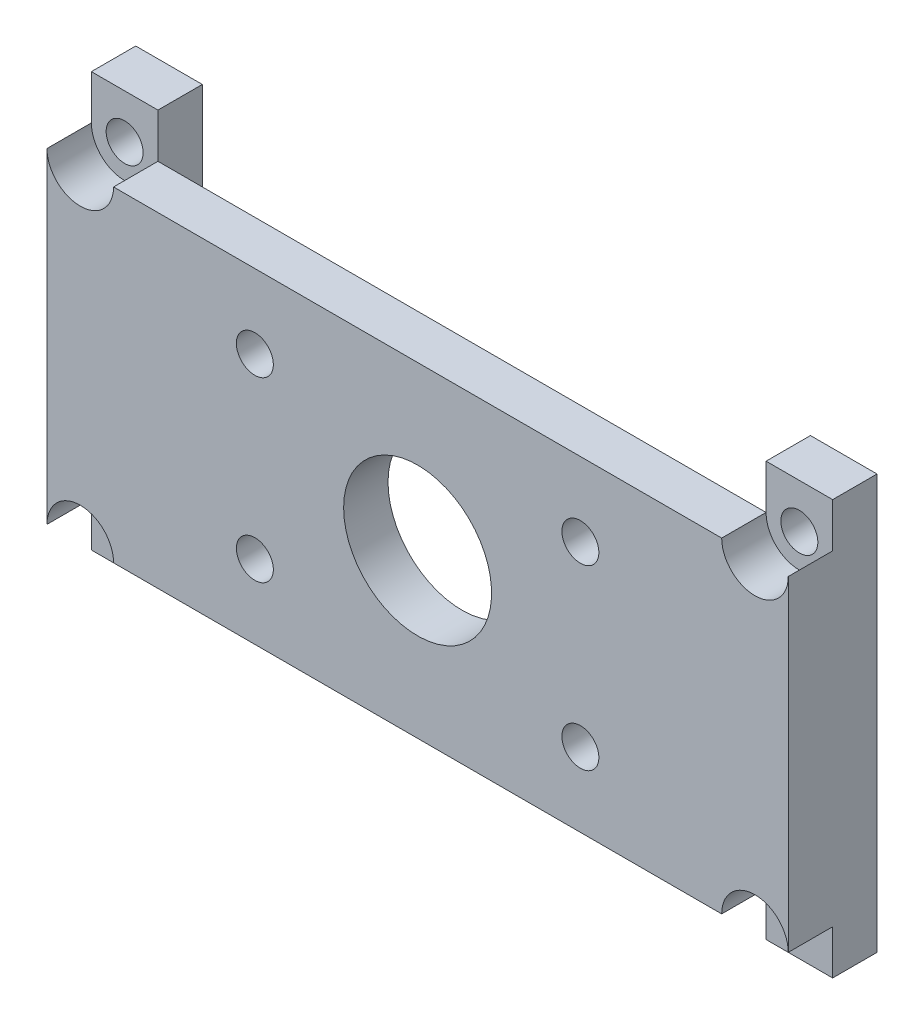
SolidWorks part; units mm, degrees
ref_plane "정면" through (0, 0, 0) normal (0, 0, 1) x (1, 0, 0)
ref_plane "윗면" through (0, 0, 0) normal (0, 1, 0) x (1, 0, 0)
ref_plane "우측면" through (0, 0, 0) normal (1, 0, 0) x (0, 0, -1)
sketch "스케치1" plane through (0, 0, 0) normal (0, 0, 1) x (1, 0, 0)
  line L1 (0, 0) -> (4.5, 0)
  line L2 (0, 0) -> (0, 28)
  line L3 (0, 28) -> (4.5, 28)
  line L4 (4.5, 0) -> (4.5, 28)
  dimension "D1" = 28
  dimension "D2" = 4.5
extrude "보스-돌출1" add sketch "스케치1" along normal blind 3
ref_plane "평면1" through (0, 0, 3) normal (0, -1, 0) x (-1, 0, 0)
sketch "스케치4" plane through (0, 0, 3) normal (0, 0, 1) x (1, 0, 0)
  line L0 (0, 28) -> (0, 0) construction
  line L1 (0, 25) -> (50.1, 25)
  line L2 (0, 25) -> (0, 3)
  line L3 (0, 3) -> (50.1, 3)
  line L4 (50.1, 25) -> (50.1, 3)
  line L5 (4.5, 28) -> (0, 28) construction
  line L6 (-7.7, 0) -> (7.7, 0) construction
  point P8 (2.25, 28)
  dimension "D1" = 50.1
  dimension "D2" = 3
  dimension "D3" = 3
extrude "보스-돌출2" add sketch "스케치4" along normal blind 3
sketch "스케치5" plane through (0, 0, 3) normal (0, 0, -1) x (-1, 0, 0)
  line L1 (-50.1, 28) -> (-45.6, 28)
  line L2 (-50.1, 28) -> (-50.1, 0)
  line L3 (-50.1, 0) -> (-45.6, 0)
  line L4 (-45.6, 28) -> (-45.6, 0)
  line L5 (-50.1, 3) -> (-50.1, 25) construction
  dimension "D1" = 4.5
extrude "보스-돌출3" add sketch "스케치5" along normal blind 3
sketch "스케치6" plane through (0, 0, 0) normal (0, 0, -1) x (-1, 0, 0)
  line L1 (-45.6, 0) -> (-45.6, 28) construction
  circle A0 centre (-47.85, 25) radius 1.25
  circle A1 centre (-47.85, 3) radius 1.25
  dimension "D1" = 2.5
  dimension "D2" = 2.5
  dimension "D3" = 2.25
  dimension "D4" = 2.25
extrude "컷-돌출2" cut sketch "스케치6" against normal through all
sketch "스케치2" plane through (0, 0, 3) normal (0, 0, 1) x (1, 0, 0)
  line L0 (4.5, 28) -> (0, 28) construction
  line L1 (0, 28) -> (0, 25) construction
  circle A0 centre (2.25, 25) radius 1.25
  circle A1 centre (2.25, 3) radius 1.25
  dimension "D1" = 2.5
  dimension "D2" = 2.5
  dimension "D4" = 3
  dimension "D5" = 2.25
  dimension "D3" = 22
extrude "컷-돌출1" cut sketch "스케치2" against normal through all
sketch "스케치7" plane through (0, 0, 3) normal (0, 0, -1) x (-1, 0, 0)
  line L2 (-52.3787, 14) -> (2.8213, 14) construction
  line L3 (-25.05, 28.9926) -> (-25.05, -2.1) construction
  circle A1 centre (-25.05, 14) radius 5
  circle A2 centre (-36.05, 20) radius 1.25
  circle A3 centre (-14.05, 20) radius 1.25
  circle A4 centre (-36.05, 8) radius 1.25
  circle A5 centre (-14.05, 8) radius 1.25
  dimension "D1" = 10
  dimension "D2" = 11
  dimension "D4" = 2.5
  dimension "D3" = 6
extrude "컷-돌출3" cut sketch "스케치7" against normal through all
sketch "스케치10" plane through (0, 0, 6) normal (0, 0, 1) x (1, 0, 0)
  line L0 (0, 3) -> (46.6, 3) construction
  circle A0 centre (2.25, 25) radius 2.25
  circle A1 centre (2.25, 3) radius 2.25
  circle A2 centre (47.85, 25) radius 2.25
  circle A3 centre (47.85, 3) radius 2.25
extrude "컷-돌출4" cut sketch "스케치10" against normal blind 3
